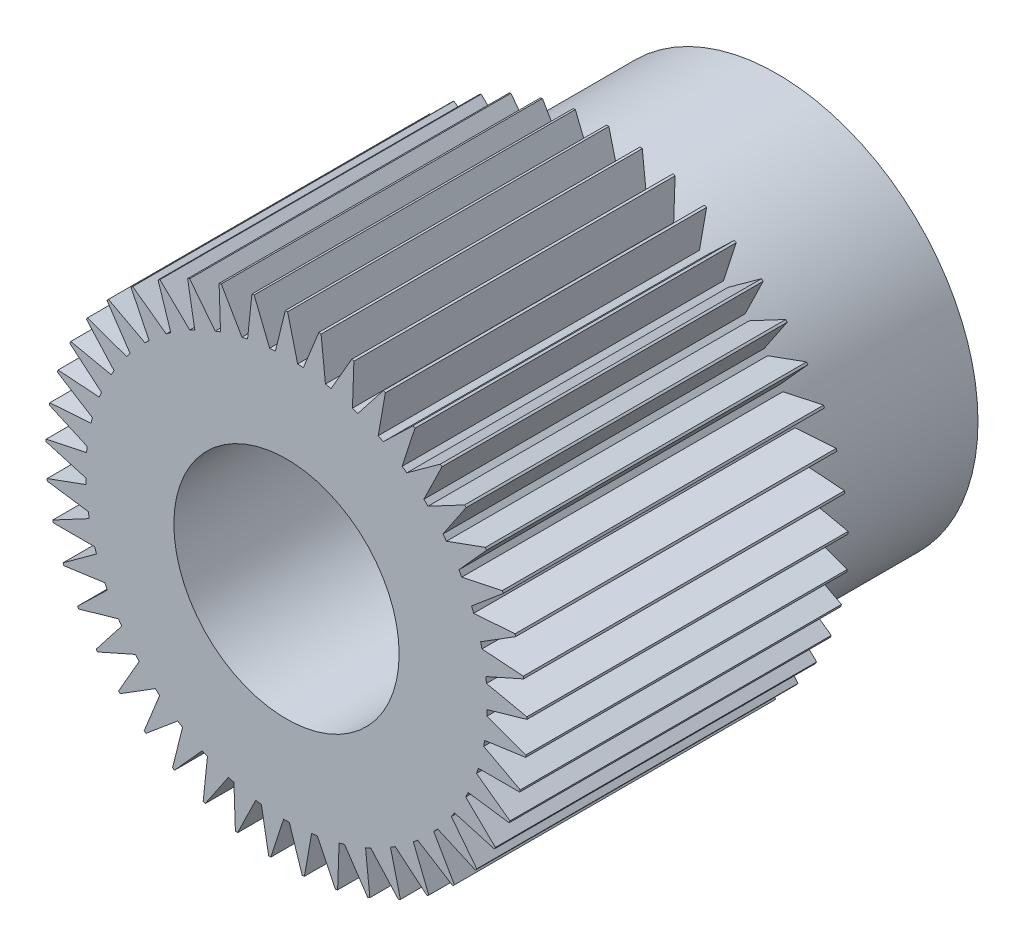
SolidWorks part; units mm, degrees
ref_plane "Front Plane" through (0, 0, 0) normal (0, 0, 1) x (1, 0, 0)
ref_plane "Top Plane" through (0, 0, 0) normal (0, 1, 0) x (1, 0, 0)
ref_plane "Right Plane" through (0, 0, 0) normal (1, 0, 0) x (0, 0, -1)
sketch "Sketch1" plane through (0, 0, 0) normal (0, 0, 1) x (1, 0, 0)
  circle A0 centre (0, 0) radius 4.5
  dimension "D1" = 9
extrude "Boss-Extrude1" add sketch "Sketch1" along normal blind 11
sketch "Sketch2" plane through (0, 0, 11) normal (0, 0, 1) x (1, 0, 0)
  circle A0 centre (0, 0) radius 2.525
  dimension "D1" = 5.05
extrude "Cut-Extrude1" cut sketch "Sketch2" against normal through all
sketch "Sketch3" plane through (0, 0, 11) normal (0, 0, 1) x (1, 0, 0)
  line L0 (-0.25, 4.4931) -> (-0.025, 5.3931)
  line L1 (0.025, 5.3931) -> (0.25, 4.4931)
  line L2 (0, 0) -> (0, 2.525) construction
  line L3 (-0.025, 5.3931) -> (0.025, 5.3931)
  circle A0 centre (0, 0) radius 4.5 construction
  circle A1 centre (0, 0) radius 2.525 construction
  arc A2 (-0.25, 4.4931) -> (0.25, 4.4931) centre (0, 0) cw
  dimension "D1" = 4.5
  dimension "D3" = 0.05
  dimension "D2" = 0.5
  dimension "D4" = 0.9
extrude "Boss-Extrude2" add sketch "Sketch3" against normal blind 7.2
pattern_circular "CirPattern2" count 45 over 360 about axis through (0, 0, 0) along (0, 0, 1) of "Boss-Extrude2"
